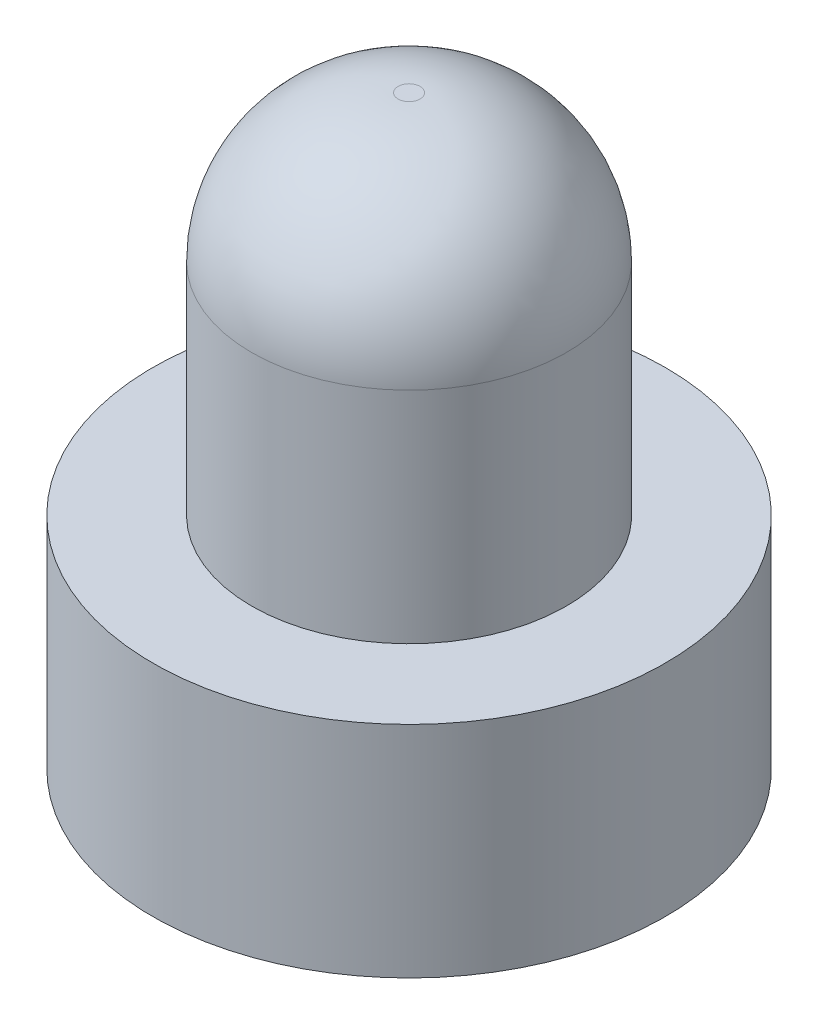
SolidWorks part; units mm, degrees
ref_plane "Front Plane" through (0, 0, 0) normal (0, 0, 1) x (1, 0, 0)
ref_plane "Top Plane" through (0, 0, 0) normal (0, 1, 0) x (1, 0, 0)
ref_plane "Right Plane" through (0, 0, 0) normal (1, 0, 0) x (0, 0, -1)
sketch "Sketch1" plane through (0, 0, 0) normal (0, 1, 0) x (1, 0, 0)
  circle A0 centre (0, 0) radius 2.15
  dimension "D1" = 4.3
extrude "Boss-Extrude1" add sketch "Sketch1" along normal blind 5
sketch "Sketch2" plane through (0, 0, 0) normal (0, -1, 0) x (1, 0, 0)
  circle A0 centre (0, 0) radius 3.5
  dimension "D1" = 7
extrude "Boss-Extrude2" add sketch "Sketch2" along normal blind 3
sketch "Sketch3" plane through (0, -3, 0) normal (0, -1, 0) x (1, 0, 0)
  circle A0 centre (0, 0) radius 2
  dimension "D1" = 4
extrude "Cut-Extrude1" cut sketch "Sketch3" against normal blind 3
fillet "Fillet1" radius 2 1 edges at (0, 5, 2.15)
